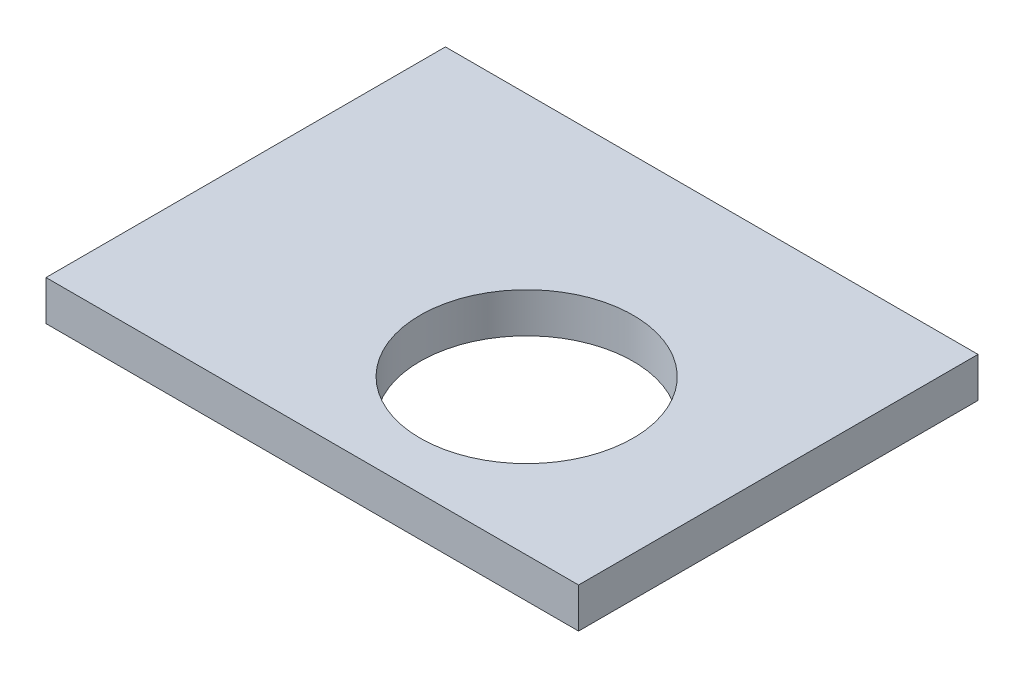
SolidWorks part; units mm, degrees
ref_plane "Front Plane" through (0, 0, 0) normal (0, 0, 1) x (1, 0, 0)
ref_plane "Top Plane" through (0, 0, 0) normal (0, 1, 0) x (1, 0, 0)
ref_plane "Right Plane" through (0, 0, 0) normal (1, 0, 0) x (0, 0, -1)
sketch "Sketch1" plane through (0, 0, 0) normal (0, 1, 0) x (1, 0, 0)
  line L1 (0, 0) -> (80, 0)
  line L2 (0, 0) -> (0, 60)
  line L3 (0, 60) -> (80, 60)
  line L4 (80, 0) -> (80, 60)
  circle A0 centre (49, 23.2) radius 16
  dimension "D3" = 32
  dimension "D5" = 49
  dimension "D1" = 80
  dimension "D2" = 60
  dimension "D4" = 36.8
extrude "Boss-Extrude1" add sketch "Sketch1" along normal blind 6
